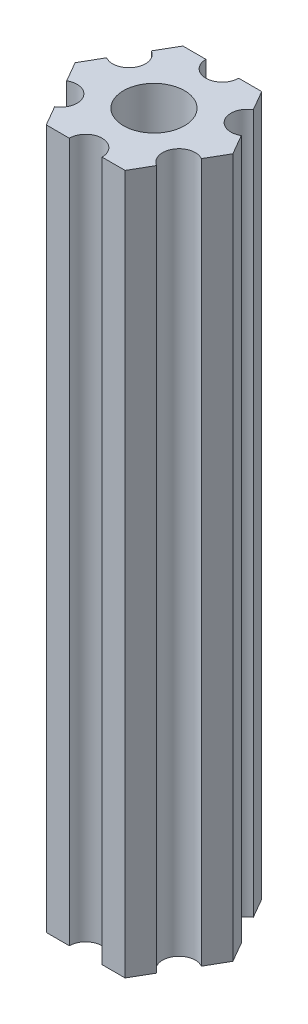
SolidWorks part; units mm, degrees
material "Churro - 6005A-T61"
ref_plane "Plano frontal" through (0, 0, 0) normal (0, 0, 1) x (1, 0, 0)
ref_plane "Plano superior" through (0, 0, 0) normal (0, 1, 0) x (1, 0, 0)
ref_plane "Plano direito" through (0, 0, 0) normal (1, 0, 0) x (0, 0, -1)
ref_plane "Plano1" through (0, 85, 0) normal (0, 1, 0) x (1, 0, 0)
sketch "Esboço1" plane through (0, 85, 0) normal (0, 1, 0) x (1, 0, 0)
  line L0 (6.1627, -1.826) -> (7.2169, 0)
  line L1 (7.2169, 0) -> (6.1627, 1.826)
  line L2 (4.6627, 4.424) -> (3.6084, 6.25)
  line L3 (3.6084, 6.25) -> (1.5, 6.25)
  line L4 (-1.5, 6.25) -> (-3.6084, 6.25)
  line L5 (-3.6084, 6.25) -> (-4.6627, 4.424)
  line L6 (-6.1627, 1.826) -> (-7.2169, 0)
  line L7 (-7.2169, 0) -> (-6.1627, -1.826)
  line L8 (-4.6627, -4.424) -> (-3.6084, -6.25)
  line L9 (-3.6084, -6.25) -> (-1.5, -6.25)
  line L10 (1.5, -6.25) -> (3.6084, -6.25)
  line L11 (3.6084, -6.25) -> (4.6627, -4.424)
  arc A0 (6.1627, 1.826) -> (4.6627, 4.424) centre (5.4127, 3.125) cw
  arc A1 (1.5, 6.25) -> (-1.5, 6.25) centre (0, 6.25) cw
  arc A2 (-4.6627, 4.424) -> (-6.1627, 1.826) centre (-5.4127, 3.125) cw
  arc A3 (-6.1627, -1.826) -> (-4.6627, -4.424) centre (-5.4127, -3.125) cw
  arc A4 (-1.5, -6.25) -> (1.5, -6.25) centre (0, -6.25) cw
  arc A5 (4.6627, -4.424) -> (6.1627, -1.826) centre (5.4127, -3.125) cw
  circle A6 centre (0, 0) radius 2.79
extrude "Ressalto-extrusão1" add sketch "Esboço1" against normal blind 64
